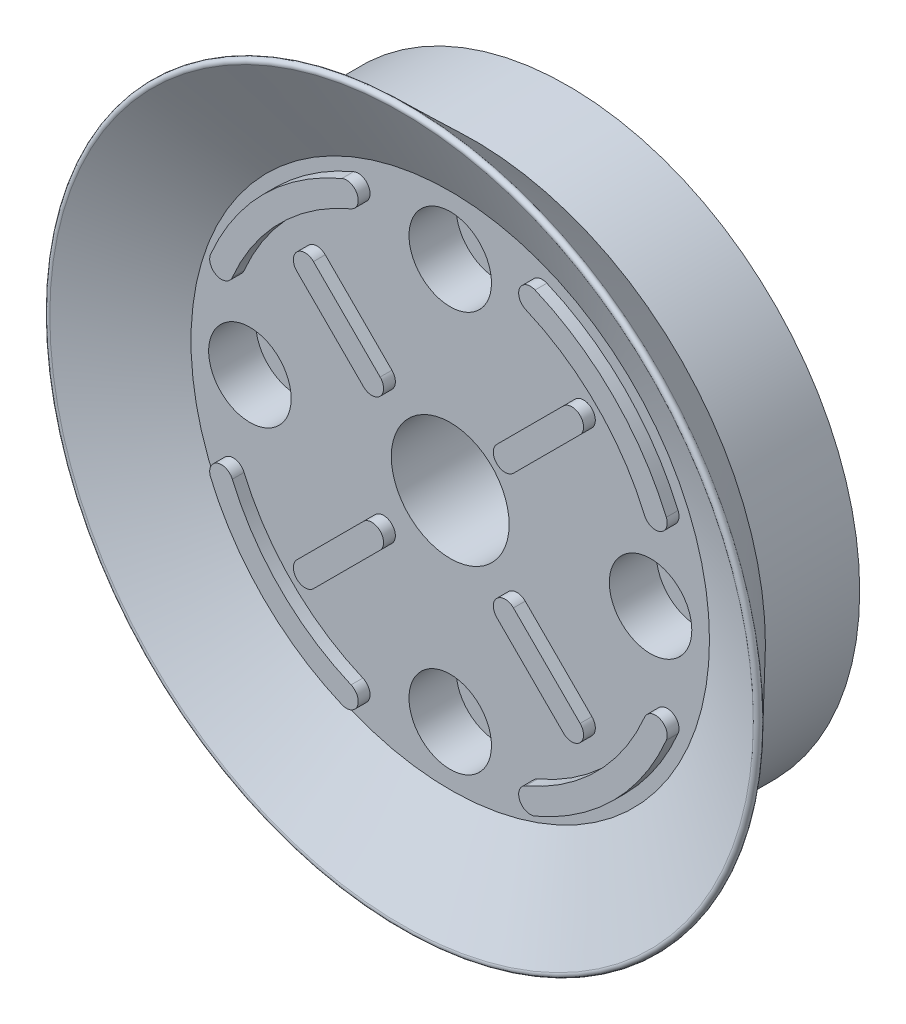
SolidWorks part; units mm, degrees
ref_plane "前视基准面" through (0, 0, 0) normal (0, 0, 1) x (1, 0, 0)
ref_plane "上视基准面" through (0, 0, 0) normal (0, 1, 0) x (1, 0, 0)
ref_plane "右视基准面" through (0, 0, 0) normal (1, 0, 0) x (0, 0, -1)
other "Configuration Table"
sketch "草图1" plane through (0, 0, 0) normal (0, 0, 1) x (1, 0, 0)
  circle A0 centre (0, 0) radius 24.75
  dimension "D1" = 49.5
extrude "凸台-拉伸1" add sketch "草图1" along normal blind 8
sketch "草图2" plane through (0, 0, 0) normal (0, 1, 0) x (1, 0, 0)
  line L0 (-24.75, -8) -> (-31.5, -15)
  line L1 (-31.5, -15) -> (-22, -10)
  line L2 (-22, -10) -> (0, -10)
  line L3 (0, -10) -> (0, -8) construction
  line L4 (-24.75, -8) -> (24.75, -8) construction
  line L5 (0, -8) -> (-24.75, -8)
  line L6 (24.75, 0) -> (-24.75, 0) construction
  line L7 (0, -10) -> (0, -8)
  point P10 (0, -10.306)
  point P11 (-23.3538, -10.6478)
  point P12 (-22, -10.817)
  dimension "D1" = 15
  dimension "D2" = 63
  dimension "D3" = 44
  dimension "D4" = 10
revolve "旋转1" add sketch "草图2" angle 360 about L3
fillet "圆角1" radius 0.3 1 edges at (31.5, 0, 15)
sketch "草图3" plane through (0, 0, 10) normal (0, 0, 1) x (1, 0, 0)
  circle A0 centre (0, 0) radius 5
  dimension "D1" = 10
extrude "切除-拉伸1" cut sketch "草图3" against normal through all both and the other way through all
sketch "草图4" plane through (0, 0, 10) normal (0, 0, 1) x (1, 0, 0)
  circle A0 centre (0, 0) radius 17
  point P3 (0, 17)
  point P5 (0, 17)
  dimension "D1" = 34
hole_wizard "孔1" positions "草图4" profile "草图5" legacy
sketch "草图5" plane through (0, 17, 10) normal (1, 0, 0) x (0, -1, 0)
  line L0 (0, 0) -> (0, 100)
  line L1 (0, 100) -> (2, 100)
  line L2 (2, 100) -> (2, 4)
  line L3 (2, 4) -> (3.5, 4)
  line L4 (3.5, 4) -> (3.5, 0)
  line L5 (3.5, 0) -> (0, 0)
  line L6 (0, 110) -> (0, -10) construction
  dimension "直径" = 4
  dimension "深度" = 100
  dimension "柱坑直径" = 7
  dimension "柱坑深度" = 4
pattern_circular "阵列(圆周)1" count 4 over 360 about axis through (0, 0, 0) along (0, 0, 1) of "孔1"
sketch "草图6" plane through (0, 0, 10) normal (0, 0, 1) x (1, 0, 0)
  line L0 (-14.1421, 14.1421) -> (0, 0) construction
  line L1 (0, 0) -> (-17, 0) construction
  arc A0 (-7.8068, 18.4134) -> (-18.4134, 7.8068) centre (0, 0) ccw construction
  arc A1 (-8.1972, 19.3341) -> (-19.3341, 8.1972) centre (0, 0) ccw
  arc A2 (-7.4165, 17.4927) -> (-17.4927, 7.4165) centre (0, 0) ccw
  arc A3 (-7.4165, 17.4927) -> (-8.1972, 19.3341) centre (-7.8068, 18.4134) ccw
  arc A4 (-19.3341, 8.1972) -> (-17.4927, 7.4165) centre (-18.4134, 7.8068) ccw
  circle A5 centre (0, 0) radius 22 construction
  point P4 (-14.1421, 14.1421)
  point P12 (-6.9008, 17.9317)
  dimension "D1" = 1
  dimension "D3" = 21
  dimension "D2" = 45
  dimension "D4" = 15
extrude "1" add sketch "草图6" along normal blind 1
sketch "草图7" plane through (0, 0, 10) normal (0, 0, 1) x (1, 0, 0)
  line L0 (-11.3137, 11.3137) -> (-5.6569, 5.6569) construction
  line L1 (-10.6066, 12.0208) -> (-4.9497, 6.364)
  line L2 (-12.0208, 10.6066) -> (-6.364, 4.9497)
  line L3 (-13.435, 13.435) -> (-11.3137, 11.3137) construction
  arc A0 (-10.6066, 12.0208) -> (-12.0208, 10.6066) centre (-11.3137, 11.3137) ccw
  arc A1 (-6.364, 4.9497) -> (-4.9497, 6.364) centre (-5.6569, 5.6569) ccw
  arc A2 (-7.4165, 17.4927) -> (-17.4927, 7.4165) centre (0, 0) ccw construction
  point P2 (-8.4853, 8.4853)
  point P7 (-8.33, 8.33)
  dimension "D1" = 1
  dimension "D2" = 8
  dimension "D3" = 8
extrude "凸台-拉伸3" add sketch "草图7" along normal blind 1
pattern_circular "阵列(圆周)2" count 4 over 360 about axis through (0, 0, 0) along (0, 0, 1) of "凸台-拉伸3", "1"
